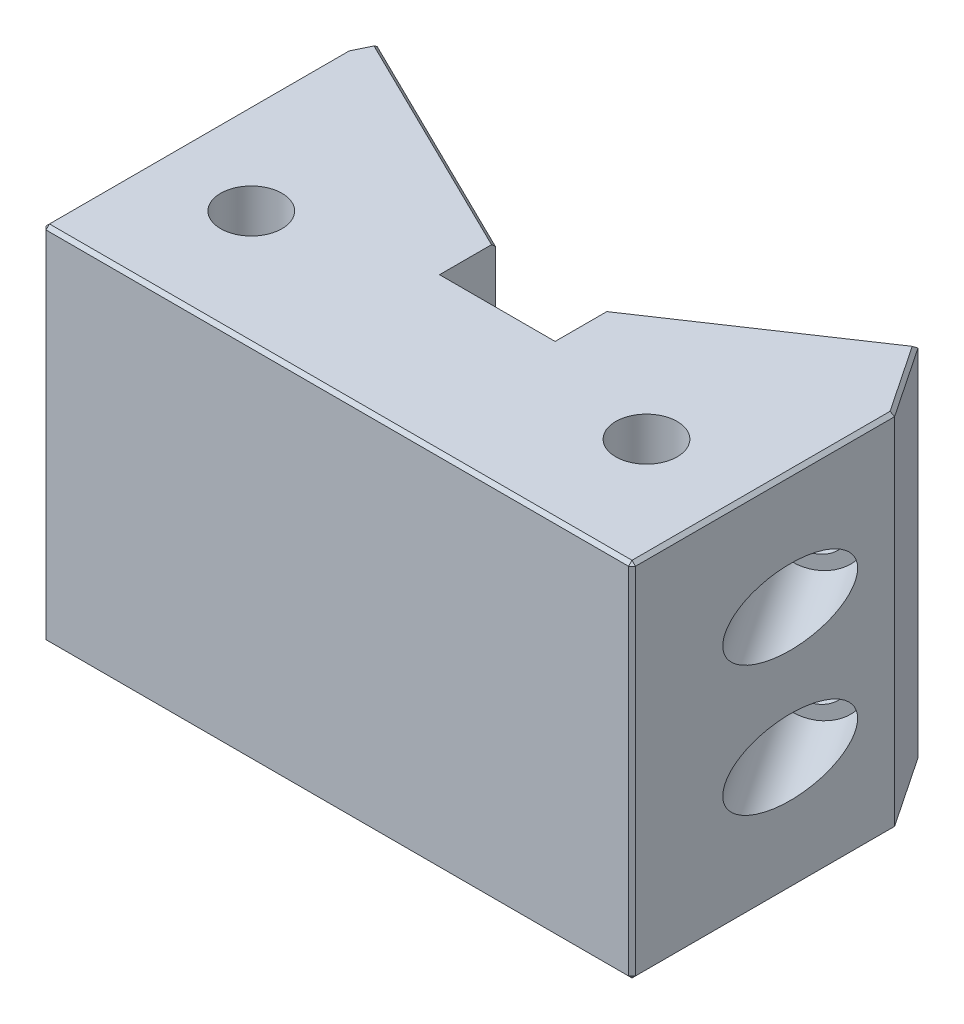
SolidWorks part; units mm, degrees
material "6061-T6 Al"
ref_plane "Front Plane" through (0, 0, 0) normal (0, 0, 1) x (1, 0, 0)
ref_plane "Top Plane" through (0, 0, 0) normal (0, 1, 0) x (1, 0, 0)
ref_plane "Right Plane" through (0, 0, 0) normal (1, 0, 0) x (0, 0, -1)
sketch "Sketch1" plane through (0, 0, 0) normal (0, 1, 0) x (1, 0, 0)
  line L0 (-64.77, 36.195) -> (-64.77, -36.195)
  line L1 (-64.77, -36.195) -> (64.77, -36.195)
  line L2 (64.77, -36.195) -> (64.77, 44.1627)
  line L3 (64.77, 44.1627) -> (3.178, 2.843)
  line L4 (3.178, 2.843) -> (-64.77, 36.195)
  line L5 (0, 0) -> (-64.77, 0) construction
  line L6 (0, 0) -> (0, -36.195) construction
  dimension "D1" = 120
  dimension "D2" = 75.692
  dimension "D3" = 74.168
  dimension "D4" = 129.54
  dimension "D5" = 72.39
extrude "Extrude1" add sketch "Sketch1" along normal blind 79.502
ref_plane "Plane1" through (-27.3575, 0, 55.7354) normal (0.4406, 0, -0.8977) x (-0.8977, 0, -0.4406)
ref_plane "Plane2" through (36.4625, 0, 54.3519) normal (-0.5571, 0, -0.8304) x (-0.8304, 0, 0.5571)
hole_wizard "CBORE for 3/8 Socket Head Cap Screw1" positions "Sketch7" profile "Sketch6" counterbore size "3/8" standard "Ansi Inch" end condition through all
sketch "Sketch7" plane through (-27.3575, 0, 55.7354) normal (0.4406, 0, -0.8977) x (-0.8977, 0, -0.4406)
  line L0 (74.0919, 79.502) -> (74.0919, 0) construction
  line L1 (74.0919, 0) -> (42.1949, 0) construction
  point P0 (58.8519, 48.26)
  point P1 (58.8519, 22.86)
  dimension "D1" = 15.24
  dimension "D2" = 15.24
  dimension "D3" = 22.86
  dimension "D4" = 48.26
sketch "Sketch6" plane through (-80.1882, 48.26, 29.8036) normal (0, 1, 0) x (0.8977, 0, 0.4406)
  line L0 (0, 0) -> (0, 130.2714)
  line L1 (0, 130.2714) -> (5.1587, 130.2714)
  line L3 (5.1587, 130.2714) -> (5.1587, 50.165)
  line L4 (5.1587, 50.165) -> (8.255, 50.165)
  line L5 (8.255, 50.165) -> (8.255, 0)
  line L7 (8.255, 0) -> (0, 0)
  line L11 (0, -6.35) -> (0, 107.95) construction
  dimension "Thru Hole Dia." = 10.3175
  dimension "Thru Hole Depth" = 130.2714
  dimension "C'Bore Dia." = 16.51
  dimension "C'Bore Depth" = 50.165
hole_wizard "CBORE for 3/8 Socket Head Cap Screw2" positions "Sketch13" profile "Sketch12" counterbore size "3/8" standard "Ansi Inch" end condition through all
sketch "Sketch13" plane through (36.4625, 0, 54.3519) normal (-0.5571, 0, -0.8304) x (-0.8304, 0, 0.5571)
  line L0 (-33.623, 0) -> (-78.391, 0) construction
  line L1 (-78.391, 79.502) -> (-78.391, 0) construction
  point P0 (-52.991, 25.4)
  point P2 (-52.991, 53.975)
  dimension "D1" = 25.4
  dimension "D2" = 53.975
  dimension "D3" = 25.4
  dimension "D4" = 25.4
sketch "Sketch12" plane through (80.4683, 25.4, 24.8301) normal (0, 1, 0) x (0.8304, 0, -0.5571)
  line L0 (0, 0) -> (0, 138.2079)
  line L1 (0, 138.2079) -> (5.1587, 138.2079)
  line L3 (5.1587, 138.2079) -> (5.1587, 50.165)
  line L4 (5.1587, 50.165) -> (8.255, 50.165)
  line L5 (8.255, 50.165) -> (8.255, 0)
  line L7 (8.255, 0) -> (0, 0)
  line L11 (0, -6.35) -> (0, 107.95) construction
  dimension "Thru Hole Dia." = 10.3175
  dimension "Thru Hole Depth" = 138.2079
  dimension "C'Bore Dia." = 16.51
  dimension "C'Bore Depth" = 50.165
sketch "Sketch14" plane through (0, 79.502, 0) normal (0, 1, 0) x (1, 0, 0)
  line L0 (3.178, 2.843) -> (-64.77, 36.195) construction
  line L1 (-11.49, 10.0427) -> (13.91, 10.0427)
  line L2 (-11.49, 10.0427) -> (-11.49, -2.237)
  line L3 (-11.49, -2.237) -> (13.91, -2.237)
  line L4 (13.91, 10.0427) -> (13.91, -2.237)
  line L5 (64.77, 44.1627) -> (3.178, 2.843) construction
  dimension "D1" = 25.4
  dimension "D2" = 5.08
extrude "Extrude2" cut sketch "Sketch14" against normal through all
hole_wizard "CBORE for 1/2 Socket Head Cap Screw1" positions "Sketch16" profile "Sketch15" counterbore size "1/2" standard "Ansi Inch" end condition through all
sketch "Sketch16" plane through (0, 0, 0) normal (0, -1, 0) x (1, 0, 0)
  line L1 (0, 36.195) -> (0, 10.795) construction
  line L2 (-64.77, 36.195) -> (64.77, 36.195) construction
  line L3 (0, 10.795) -> (-44.2976, 10.795) construction
  line L4 (0, 10.795) -> (42.545, 10.795) construction
  point P0 (-44.2976, 10.795)
  point P1 (42.545, 10.795)
  dimension "D1" = 44.2976
  dimension "D2" = 25.4
  dimension "D3" = 42.545
sketch "Sketch15" plane through (-44.2976, 0, 10.795) normal (1, 0, 0) x (0, 0, -1)
  line L0 (0, 0) -> (0, 79.502)
  line L1 (0, 79.502) -> (6.7462, 79.502)
  line L3 (6.7462, 79.502) -> (6.7462, 68.58)
  line L4 (6.7462, 68.58) -> (10.3187, 68.58)
  line L5 (10.3187, 68.58) -> (10.3187, 0)
  line L7 (10.3187, 0) -> (0, 0)
  line L11 (0, -6.35) -> (0, 107.95) construction
  dimension "Thru Hole Dia." = 13.4925
  dimension "Thru Hole Depth" = 79.502
  dimension "C'Bore Dia." = 20.6375
  dimension "C'Bore Depth" = 68.58
sketch "Sketch17" plane through (0, 0, 0) normal (0, -1, 0) x (1, 0, 0)
  line L1 (-64.77, -30.6092) -> (-62.5606, -35.1105)
  line L2 (-64.77, -36.195) -> (-64.77, 36.195) construction
  line L3 (-11.49, -10.0427) -> (-64.77, -36.195) construction
  line L4 (-62.5606, -35.1105) -> (-64.77, -36.195)
  line L6 (-64.77, -36.195) -> (-64.77, -30.6092)
  line L7 (64.77, -44.1627) -> (54.2888, -37.1313)
  line L8 (64.77, -44.1627) -> (13.91, -10.0427) construction
  line L9 (54.2888, -37.1313) -> (64.77, -21.5077)
  line L10 (64.77, 36.195) -> (64.77, -44.1627) construction
  line L11 (64.77, -21.5077) -> (64.77, -44.1627)
  line L13 (-62.7151, -17.5021) -> (-55.7202, -31.7529) construction
  line L14 (47.9609, -32.8861) -> (56.805, -19.7029) construction
  dimension "D1" = 7.62
  dimension "D2" = 7.62
extrude "Extrude3" cut sketch "Sketch17" against normal through all
chamfer "Chamfer1" distance 0.762 angle 45 18 edges at (54.2888, 39.751, -37.1313) (59.5294, 0, -29.3195) (34.0994, 79.502, -23.587) (59.5294, 79.502, -29.3195) (-37.0253, 79.502, -22.5766) (-63.6653, 79.502, -32.8598) (-64.77, 79.502, 2.7929) (-64.77, 0, 2.7929) (-64.77, 39.751, 36.195) (0, 79.502, 36.195) (64.77, 79.502, 7.3436) (64.77, 39.751, 36.195) (0, 0, 36.195) (64.77, 0, 7.3436) (-37.0253, 0, -22.5766) (34.0994, 0, -23.587) (-62.5606, 39.751, -35.1105) (-63.6653, 0, -32.8598)
